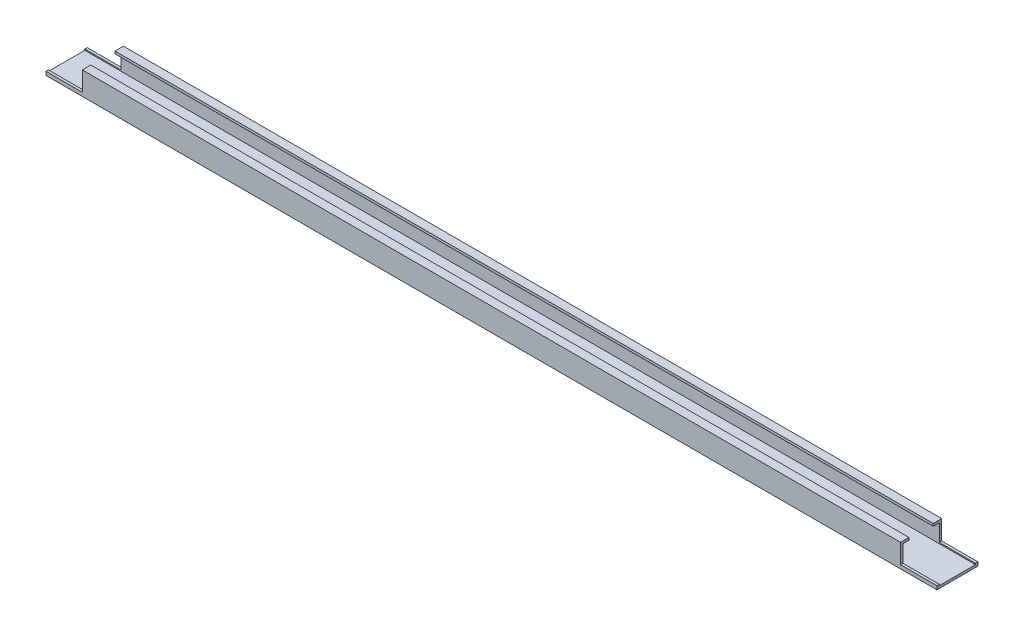
SolidWorks part; units mm, degrees
ref_plane "Спереди" through (0, 0, 0) normal (0, 0, 1) x (1, 0, 0)
ref_plane "Сверху" through (0, 0, 0) normal (0, 1, 0) x (1, 0, 0)
ref_plane "Справа" through (0, 0, 0) normal (1, 0, 0) x (0, 0, -1)
sketch "Эскиз1" plane through (0, 0, 0) normal (1, 0, 0) x (0, 0, -1)
  line L0 (-15, 0) -> (15, 0)
  line L1 (15, 0) -> (15, 15)
  line L2 (15, 15) -> (10, 15)
  line L3 (-15, 0) -> (-15, 15)
  line L4 (-15, 15) -> (-10, 15)
extrude "Вытянуть-Тонкостенный1" add sketch "Эскиз1" along normal blind 736 thin
sketch "Эскиз2" plane through (0, 0, -17) normal (0, 0, -1) x (-1, 0, 0)
  line L1 (-736, 17) -> (-706, 17)
  line L2 (-736, 17) -> (-736, 1)
  line L3 (-736, 1) -> (-706, 1)
  line L4 (-706, 17) -> (-706, 1)
  line L5 (0, 17) -> (-30, 17)
  line L6 (0, 17) -> (0, 1)
  line L7 (0, 1) -> (-30, 1)
  line L8 (-30, 17) -> (-30, 1)
  point P9 (-708.6961, 2.3919)
  point P10 (-686.9907, 17)
extrude "Вырез-Вытянуть1" cut sketch "Эскиз2" against normal through all
